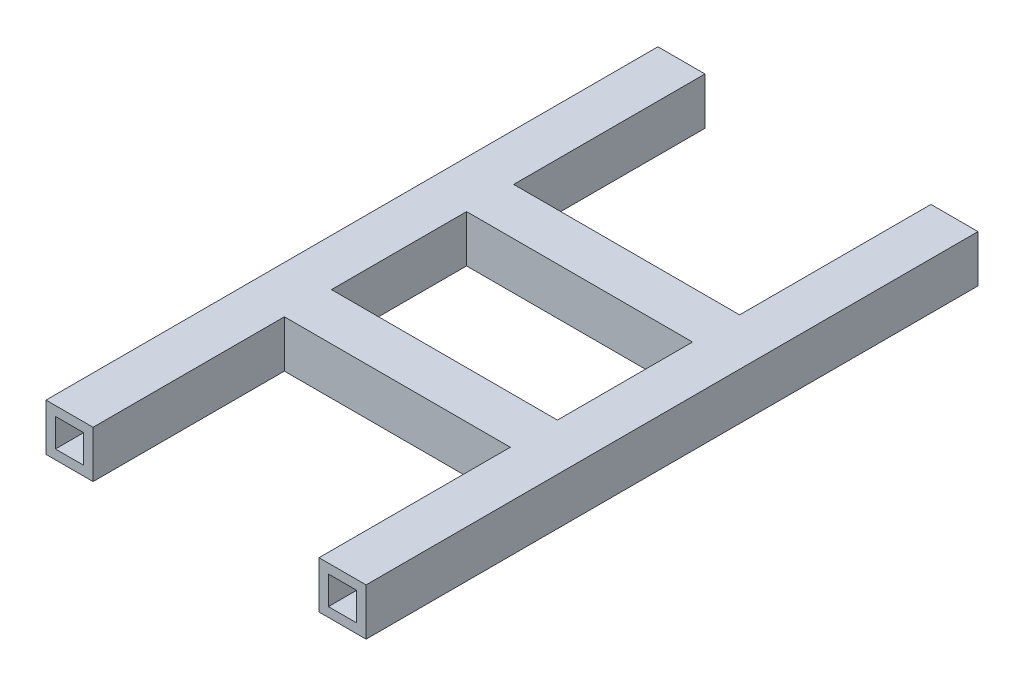
SolidWorks part; units mm, degrees
ref_plane "Front Plane" through (0, 0, 0) normal (0, 0, 1) x (1, 0, 0)
ref_plane "Top Plane" through (0, 0, 0) normal (0, 1, 0) x (1, 0, 0)
ref_plane "Right Plane" through (0, 0, 0) normal (1, 0, 0) x (0, 0, -1)
sketch "Sketch1" plane through (0, 0, 0) normal (0, 0, 1) x (1, 0, 0)
  line L0 (-25, 25) -> (25, 25)
  line L1 (-15, -15) -> (15, -15)
  line L2 (-15, -15) -> (-15, 15)
  line L3 (-15, 15) -> (15, 15)
  line L4 (15, -15) -> (15, 15)
  line L5 (-15, -15) -> (15, 15) construction
  line L6 (-15, 15) -> (15, -15) construction
  line L11 (25, -25) -> (25, 25)
  line L12 (-25, -25) -> (25, -25)
  line L13 (-25, -25) -> (-25, 25)
  line L14 (265, 25) -> (315, 25)
  line L15 (275, -15) -> (305, -15)
  line L16 (275, -15) -> (275, 15)
  line L17 (275, 15) -> (305, 15)
  line L18 (305, -15) -> (305, 15)
  line L19 (275, -15) -> (305, 15) construction
  line L20 (275, 15) -> (305, -15) construction
  line L21 (315, -25) -> (315, 25)
  line L22 (265, -25) -> (315, -25)
  line L23 (265, -25) -> (265, 25)
  point P0 (0, 0)
  point P10 (282.9842, -19.2284)
  dimension "D1" = 30
  dimension "D2" = 30
  dimension "D4" = 30
  dimension "D5" = 30
  dimension "D6" = 340
  dimension "D3" = 10
extrude "Boss-Extrude1" add sketch "Sketch1" along normal blind 650
sketch "Sketch2" plane through (0, -25, 0) normal (0, -1, 0) x (1, 0, 0)
  line L0 (265, 650) -> (315, 650) construction
  line L1 (265, 325) -> (315, 325) construction
  line L2 (265, 650) -> (265, 0) construction
  line L3 (315, 650) -> (315, 0) construction
  line L4 (25, 325) -> (265, 325) construction
  line L5 (25, 650) -> (25, 0) construction
  line L6 (145, 325) -> (145, 247.8157) construction
  circle A0 centre (290, 600) radius 10
  circle A2 centre (290, 550) radius 10
  circle A3 centre (290, 500) radius 10
  circle A4 centre (290, 150) radius 10
  circle A5 centre (290, 100) radius 10
  circle A6 centre (290, 50) radius 10
  circle A7 centre (0, 500) radius 10
  circle A8 centre (0, 550) radius 10
  circle A9 centre (0, 600) radius 10
  circle A10 centre (0, 50) radius 10
  circle A11 centre (0, 100) radius 10
  circle A12 centre (0, 150) radius 10
  dimension "D1" = 50
  dimension "D2" = 3
extrude "Cut-Extrude1" cut sketch "Sketch2" against normal blind 13 and the other way blind 18
sketch "Sketch3" plane through (265, 0, 0) normal (-1, 0, 0) x (0, 0, 1)
  line L0 (325, 25) -> (325, -25) construction
  line L1 (650, 25) -> (0, 25) construction
  line L2 (650, -25) -> (0, -25) construction
  line L3 (446.771, 25) -> (446.771, -25)
  line L4 (396.771, -25) -> (396.771, 25)
  line L5 (396.771, 25) -> (446.771, 25)
  line L6 (396.771, -25) -> (446.771, -25)
  line L7 (436.771, 15) -> (436.771, -15)
  line L8 (406.771, -15) -> (436.771, -15)
  line L9 (406.771, -15) -> (406.771, 15)
  line L10 (406.771, 15) -> (436.771, 15)
  line L11 (243.229, 15) -> (213.229, 15)
  line L12 (243.229, -15) -> (243.229, 15)
  line L13 (243.229, -15) -> (213.229, -15)
  line L14 (213.229, 15) -> (213.229, -15)
  line L15 (253.229, -25) -> (203.229, -25)
  line L16 (253.229, 25) -> (203.229, 25)
  line L17 (253.229, -25) -> (253.229, 25)
  line L18 (203.229, 25) -> (203.229, -25)
  dimension "D1" = 10
extrude "Boss-Extrude3" add sketch "Sketch3" along normal blind 240
